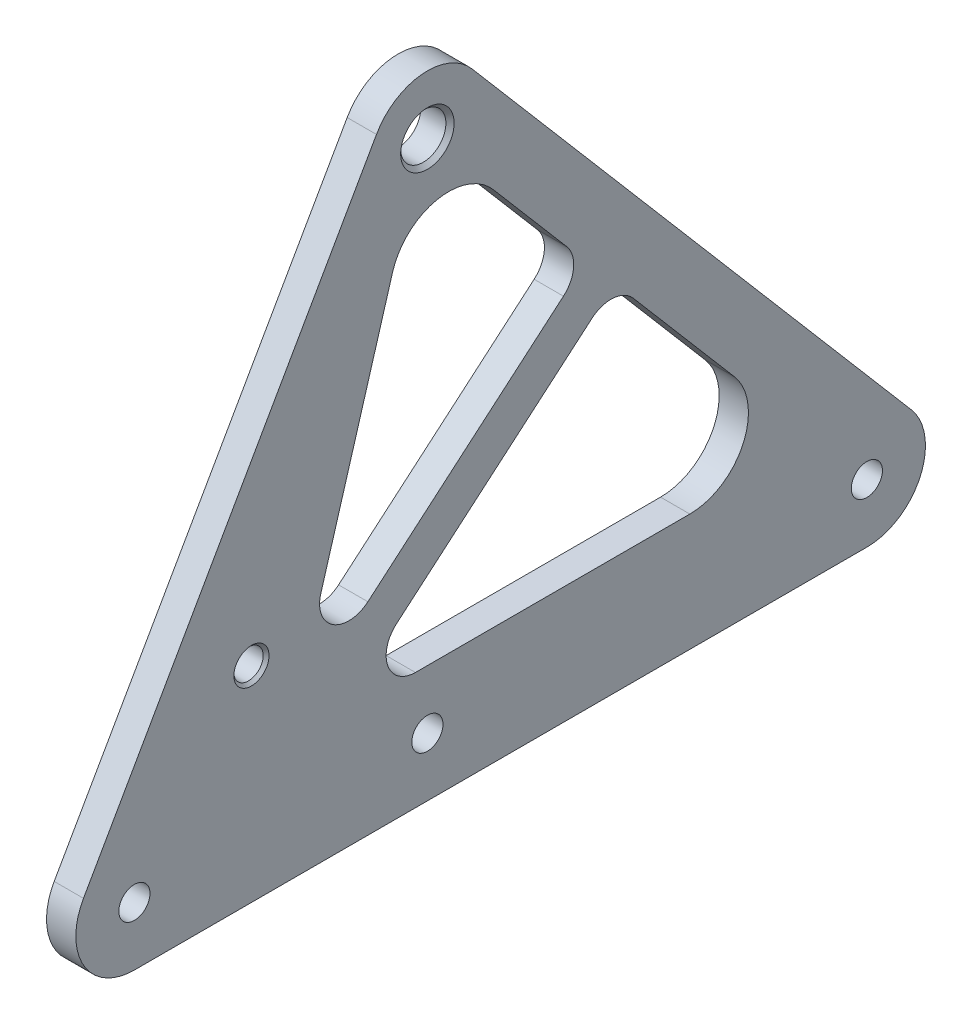
SolidWorks part; units mm, degrees
material "1060 Alloy"
ref_plane "Front Plane" through (0, 0, 0) normal (0, 0, 1) x (1, 0, 0)
ref_plane "Top Plane" through (0, 0, 0) normal (0, 1, 0) x (1, 0, 0)
ref_plane "Right Plane" through (0, 0, 0) normal (1, 0, 0) x (0, 0, -1)
sketch "Sketch1" plane through (0, 0, 0) normal (1, 0, 0) x (0, 0, -1)
  line L0 (-74.539, -105.3537) -> (-11.039, 6.2793)
  line L1 (9.6612, 8.2433) -> (104.9112, -103.3897)
  line L2 (-63.5, -124.333) -> (95.25, -124.333)
  arc A0 (9.6612, 8.2433) -> (-11.039, 6.2793) centre (0, 0) ccw
  arc A1 (95.25, -124.333) -> (104.9112, -103.3897) centre (95.25, -111.633) ccw
  arc A2 (-74.539, -105.3537) -> (-63.5, -124.333) centre (-63.5, -111.633) ccw
  dimension "D1" = 158.75
  dimension "D2" = 111.633
  dimension "D4" = 25.4
  dimension "D5" = 95.25
extrude "Boss-Extrude1" add sketch "Sketch1" along normal blind 6.35 contours L1 A1 L2 A2 L0 A0
sketch "Sketch2" plane through (6.35, 0, 0) normal (1, 0, 0) x (0, 0, -1)
  circle A0 centre (-63.5, -111.633) radius 3.3782
  circle A1 centre (0, -111.633) radius 3.3782
  circle A2 centre (95.25, -111.633) radius 3.3782
  arc A3 (-74.539, -105.3537) -> (-63.5, -124.333) centre (-63.5, -111.633) ccw construction
  arc A4 (95.25, -124.333) -> (104.9112, -103.3897) centre (95.25, -111.633) ccw construction
  dimension "D2" = 0
  dimension "D3" = 0
  dimension "D4" = 63.5
  dimension "D5" = 6.7564
extrude "Cut-Extrude1" cut sketch "Sketch2" against normal up to next
hole_wizard "3/8 Clearance Hole1" positions "Sketch3" profile "Sketch4" hole size "3/8" standard "ANSI Inch" end condition through all
sketch "Sketch3" plane through (6.35, 0, 0) normal (1, 0, 0) x (0, 0, -1)
  point P0 (0, 0)
sketch "Sketch4" plane through (6.35, 0, 0) normal (0, 1, 0) x (0, 0, -1)
  line L0 (0, 0) -> (0, 6.35)
  line L1 (0, 6.35) -> (4.9022, 6.35)
  line L2 (4.9022, 6.35) -> (4.9022, 0.8915)
  line L3 (4.9022, 0.8915) -> (5.7937, 0)
  line L5 (5.7937, 0) -> (0, 0)
  line L6 (-4.9022, 0.8915) -> (-5.7937, 0) construction
  line L11 (0, -6.35) -> (0, 107.95) construction
  dimension "Thru Hole Dia." = 9.8044
  dimension "Thru Hole Depth" = 6.35
  dimension "Near C'Sink Dia." = 11.5875
  dimension "Near C'Sink Angle" = 90
hole_wizard "1/4 (0.2500) Dowel Hole1" positions "Sketch5" profile "Sketch6" hole size "1/4" standard "ANSI Inch" end condition through all
sketch "Sketch5" plane through (6.35, 0, 0) normal (1, 0, 0) x (0, 0, -1)
  line L0 (-63.5, -124.333) -> (95.25, -124.333) construction
  line L1 (-74.539, -105.3537) -> (-11.039, 6.2793) construction
  point P0 (-38.1343, -79.883)
  dimension "D1" = 44.45
  dimension "D2" = 19.05
sketch "Sketch6" plane through (6.35, -79.883, 38.1343) normal (0, 1, 0) x (0, 0, -1)
  line L0 (0, 0) -> (0, 6.35)
  line L1 (0, 6.35) -> (3.175, 6.35)
  line L2 (3.175, 6.35) -> (3.175, 0.635)
  line L3 (3.175, 0.635) -> (3.81, 0)
  line L5 (3.81, 0) -> (0, 0)
  line L6 (-3.175, 0.635) -> (-3.81, 0) construction
  line L11 (0, -6.35) -> (0, 107.95) construction
  dimension "Thru Hole Dia." = 6.35
  dimension "Thru Hole Depth" = 6.35
  dimension "Near C'Sink Dia." = 7.62
  dimension "Near C'Sink Angle" = 90
sketch "Sketch7" plane through (6.35, 0, 0) normal (1, 0, 0) x (0, 0, -1)
  line L0 (-7.5605, -21.3706) -> (-23.1091, -73.8728)
  line L1 (-2.5947, -98.933) -> (56.883, -98.933)
  line L2 (66.5441, -77.9897) -> (44.6214, -52.2962)
  line L3 (-12.8989, -80.5066) -> (29.4867, -44.3414)
  line L4 (-6.7164, -87.7524) -> (35.6691, -51.5873)
  line L5 (30.1956, -35.3892) -> (14.2778, -16.7336)
  line L6 (9.6612, 8.2433) -> (104.9112, -103.3897) construction
  line L7 (-63.5, -124.333) -> (95.25, -124.333) construction
  line L9 (-17.0205, -75.676) -> (-2.5947, -92.583) construction
  arc A0 (14.2778, -16.7336) -> (-7.5605, -21.3706) centre (4.6167, -24.9769) ccw
  arc A1 (56.883, -98.933) -> (66.5441, -77.9897) centre (56.883, -86.233) ccw
  arc A4 (30.1956, -35.3892) -> (29.4867, -44.3414) centre (25.365, -39.5109) cw
  arc A6 (44.6214, -52.2962) -> (35.6691, -51.5873) centre (39.7908, -56.4179) ccw
  arc A7 (-2.5947, -98.933) -> (-6.7164, -87.7524) centre (-2.5947, -92.583) cw
  arc A8 (-12.8989, -80.5066) -> (-23.1091, -73.8728) centre (-17.0205, -75.676) cw
  circle A11 centre (-38.1343, -79.883) radius 12.7 construction
  arc A13 (9.6612, 8.2433) -> (-11.039, 6.2793) centre (0, 0) ccw construction
  point P12 (34.3172, -40.2198)
  dimension "D1" = 12.7
  dimension "D2" = 25.4
  dimension "D3" = 25.4
  dimension "D4" = 6.35
  dimension "D5" = 9.525
  dimension "D6" = 12.7
extrude "Cut-Extrude2" cut sketch "Sketch7" against normal through all
